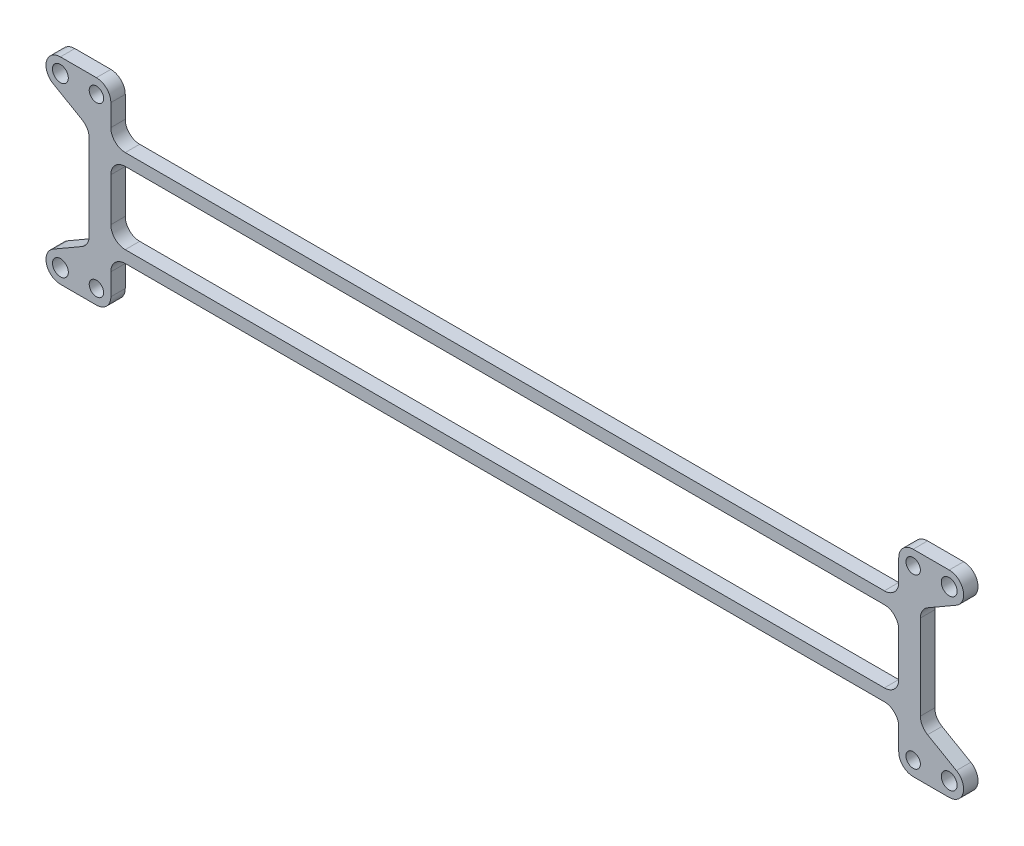
SolidWorks part; units mm, degrees
ref_plane "Plano frontal" through (0, 0, 0) normal (0, 0, 1) x (1, 0, 0)
ref_plane "Plano superior" through (0, 0, 0) normal (0, 1, 0) x (1, 0, 0)
ref_plane "Plano direito" through (0, 0, 0) normal (1, 0, 0) x (0, 0, -1)
sketch "Esboço1" plane through (0, 0, 0) normal (0, 0, 1) x (1, 0, 0)
  line L1 (-92.5, -20.5) -> (-85, -20.5)
  line L2 (-82, -17.5) -> (-82, -13)
  line L3 (-79, -10) -> (0, -10)
  line L5 (0, 10) -> (-79, 10)
  line L6 (-82, 13) -> (-82, 17.5)
  line L7 (-85, 20.5) -> (-92.5, 20.5)
  line L8 (0, 24.5963) -> (0, 0) construction
  line L9 (0, 0) -> (-13.1309, 0) construction
  line L10 (0, 7.5) -> (-79, 7.5)
  line L11 (-82, 4.5) -> (-82, -4.5)
  line L12 (-79, -7.5) -> (0, -7.5)
  line L13 (0, 10) -> (0, 7.5)
  line L14 (0, -7.5) -> (0, -10)
  line L15 (-94, 14.9019) -> (-88, 11.4378)
  line L16 (-86.5, 8.8397) -> (-86.5, -8.8397)
  line L17 (-94, -14.9019) -> (-88, -11.4378)
  circle A0 centre (-92.5, 17.5) radius 1.65
  circle A1 centre (-92.5, -17.5) radius 1.65
  circle A2 centre (-85, 17.5) radius 1.5
  circle A3 centre (-85, -17.5) radius 1.5
  arc A4 (-94, -14.9019) -> (-92.5, -20.5) centre (-92.5, -17.5) ccw
  arc A5 (-94, 14.9019) -> (-92.5, 20.5) centre (-92.5, 17.5) cw
  arc A6 (-79, 10) -> (-82, 13) centre (-79, 13) cw
  arc A7 (-79, 7.5) -> (-82, 4.5) centre (-79, 4.5) ccw
  arc A8 (-82, -13) -> (-79, -10) centre (-79, -13) cw
  arc A9 (-82, -4.5) -> (-79, -7.5) centre (-79, -4.5) ccw
  arc A10 (-85, -20.5) -> (-82, -17.5) centre (-85, -17.5) ccw
  arc A11 (-82, 17.5) -> (-85, 20.5) centre (-85, 17.5) ccw
  arc A14 (-88, -11.4378) -> (-86.5, -8.8397) centre (-89.5, -8.8397) ccw
  arc A15 (-88, 11.4378) -> (-86.5, 8.8397) centre (-89.5, 8.8397) cw
  point P0 (-80, 15.5)
  point P22 (-94.6465, 20.3993)
  point P28 (-86.5, 0)
  point P29 (-88.5, 15)
  point P33 (-94.4519, 21.045)
  point P50 (0, 0)
  point P54 (-86.5, -10.5718)
  point P57 (-86.5, 10.5718)
  point P58 (-94.6213, 19.9652)
  point P59 (0, 0)
  point P60 (0, 0)
  point P61 (-95.4264, 22.5768)
  point P62 (0, 0)
  point P63 (-92.4096, 22.5)
  dimension "D1" = 3.3
  dimension "D2" = 3
  dimension "D3" = 60
  dimension "D4" = 3
  dimension "D12" = 3
  dimension "D13" = 3
  dimension "D18" = 3
  dimension "D6" = 20
  dimension "D7" = 2.5
  dimension "D8" = 185
  dimension "D9" = 170
  dimension "D10" = 35
  dimension "D15" = 6
extrude "Ressalto-extrusão1" add sketch "Esboço1" along normal blind 3
sketch "Esboço3" plane through (0, 0, 3) normal (0, 0, 1) x (1, 0, 0)
  line L0 (0, 0) -> (-14.3805, 0) construction
  circle A0 centre (-85, 17.5) radius 3
  arc A1 (-82, 17.5) -> (-85, 20.5) centre (-85, 17.5) ccw construction
  circle A2 centre (-85, 17.5) radius 1.5 construction
  circle A3 centre (-85, 17.5) radius 1.5
  circle A4 centre (-85, -17.5) radius 1.5
  circle A5 centre (-85, -17.5) radius 3
extrude "Ressalto-extrusão2" [suppressed] add sketch "Esboço3" along normal blind 2
mirror "Espelhar1" about plane through (0, 0, 0) normal (1, 0, 0) of "Ressalto-extrusão1"
